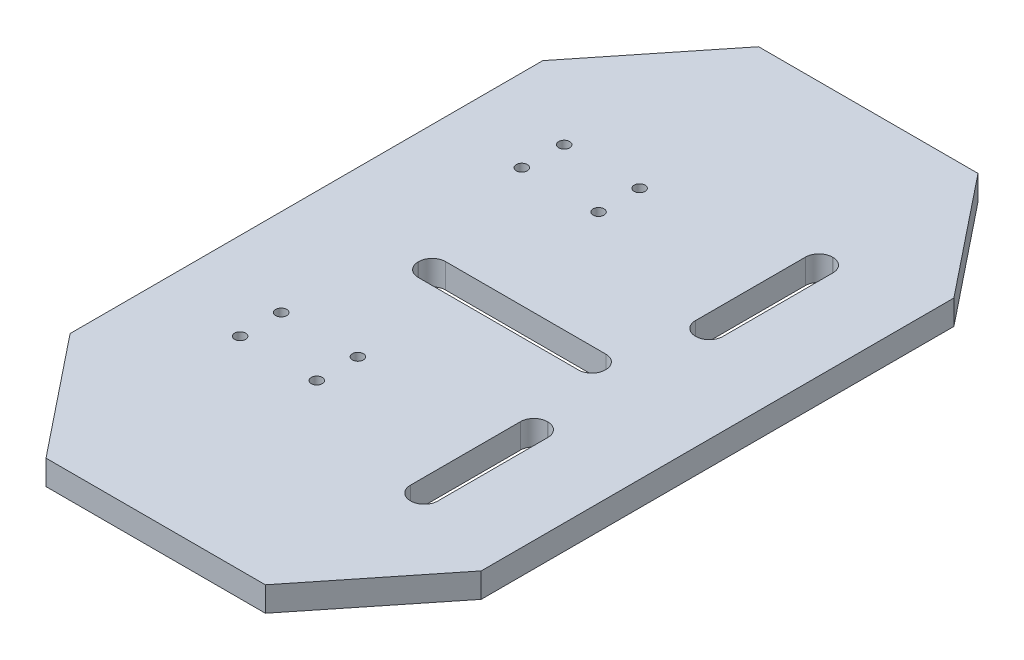
SolidWorks part; units mm, degrees
material "ABS"
ref_plane "Front Plane" through (0, 0, 0) normal (0, 0, 1) x (1, 0, 0)
ref_plane "Top Plane" through (0, 0, 0) normal (0, 1, 0) x (1, 0, 0)
ref_plane "Right Plane" through (0, 0, 0) normal (1, 0, 0) x (0, 0, -1)
other "Center of Mass"
sketch "Sketch1" plane through (0, 0, 0) normal (0, 1, 0) x (1, 0, 0)
  line L0 (-37.5, -43.1177) -> (-20.0119, -65)
  line L1 (-20.0119, -65) -> (20.0119, -65)
  line L2 (-37.5, -43.1177) -> (-37.5, 43.1177)
  line L3 (-20.0119, 65) -> (20.0119, 65)
  line L4 (37.5, -43.1177) -> (37.5, 43.1177)
  line L5 (-30.8066, -51.493) -> (30.8066, 51.493) construction
  line L6 (-32.7951, 49.0048) -> (32.7951, -49.0048) construction
  line L7 (-114.8204, 0) -> (150.9847, 0) construction
  line L8 (0, -72.5189) -> (0, 84.1411) construction
  line L9 (37.5, -43.1177) -> (20.0119, -65)
  line L10 (37.5, 43.1177) -> (20.0119, 65)
  line L11 (-37.5, 43.1177) -> (-20.0119, 65)
  point P0 (0, 0)
  dimension "D1" = 75
  dimension "D2" = 130
  dimension "D3" = 40.0238
  dimension "D4" = 86.2354
extrude "Boss-Extrude1" add sketch "Sketch1" along normal blind 4.5
sketch "Sketch5" plane through (0, 4.5, 0) normal (0, 1, 0) x (1, 0, 0)
  line L0 (-100.8141, 0) -> (111.641, 0) construction
  line L1 (20, 65) -> (20, -65) construction
  line L2 (-14.6202, -2.5) -> (14.6202, -2.5)
  line L3 (-17.0702, -0.05) -> (-17.0702, 0.05)
  line L4 (-14.6202, 2.5) -> (14.6202, 2.5)
  line L5 (17.0702, -0.05) -> (17.0702, 0.05)
  line L6 (-17.0702, -2.5) -> (17.0702, 2.5) construction
  line L7 (-17.0702, 2.5) -> (17.0702, -2.5) construction
  line L8 (20.0119, 65) -> (-20.0119, 65) construction
  line L9 (-20.0119, -65) -> (20.0119, -65) construction
  line L10 (20, 65) -> (20, 0) construction
  line L11 (20, 0) -> (20, -65) construction
  line L12 (19.95, -38.5) -> (20.05, -38.5)
  line L13 (19.95, 13.5) -> (20.05, 13.5)
  line L14 (17.5, 15.95) -> (17.5, 36.05)
  line L15 (19.95, 38.5) -> (20.05, 38.5)
  line L16 (22.5, 15.95) -> (22.5, 36.05)
  line L17 (17.5, 13.5) -> (22.5, 38.5) construction
  line L18 (17.5, 38.5) -> (22.5, 13.5) construction
  line L19 (17.5, -15.95) -> (17.5, -36.05)
  line L20 (19.95, -13.5) -> (20.05, -13.5)
  line L21 (22.5, -15.95) -> (22.5, -36.05)
  line L22 (37.5, -43.1177) -> (37.5, 43.1177) construction
  arc A0 (19.95, -38.5) -> (17.5, -36.05) centre (19.95, -36.05) cw
  arc A1 (20.05, -38.5) -> (22.5, -36.05) centre (20.05, -36.05) ccw
  arc A2 (17.5, -15.95) -> (19.95, -13.5) centre (19.95, -15.95) cw
  arc A3 (20.05, -13.5) -> (22.5, -15.95) centre (20.05, -15.95) cw
  arc A4 (-14.6202, -2.5) -> (-17.0702, -0.05) centre (-14.6202, -0.05) cw
  arc A5 (-17.0702, 0.05) -> (-14.6202, 2.5) centre (-14.6202, 0.05) cw
  arc A6 (14.6202, 2.5) -> (17.0702, 0.05) centre (14.6202, 0.05) cw
  arc A7 (14.6202, -2.5) -> (17.0702, -0.05) centre (14.6202, -0.05) ccw
  arc A8 (20.05, 13.5) -> (22.5, 15.95) centre (20.05, 15.95) ccw
  arc A9 (19.95, 13.5) -> (17.5, 15.95) centre (19.95, 15.95) cw
  arc A10 (17.5, 36.05) -> (19.95, 38.5) centre (19.95, 36.05) cw
  arc A11 (20.05, 38.5) -> (22.5, 36.05) centre (20.05, 36.05) cw
  point P3 (0, 0)
  point P14 (20, 0)
  point P15 (20, 26)
  point P17 (20, -26)
  point P18 (20, 26)
  point P31 (17.5, -38.5)
  point P34 (22.5, -38.5)
  point P37 (17.5, -13.5)
  point P40 (22.5, -13.5)
  dimension "D7" = 2.45
  dimension "D1" = 5
  dimension "D2" = 26
  dimension "D3" = 26
  dimension "D4" = 5
  dimension "D5" = 25
  dimension "D6" = 15
extrude "Cut-Extrude2" cut sketch "Sketch5" against normal blind 10
sketch "Sketch7" plane through (0, 4.5, 0) normal (0, 1, 0) x (1, 0, 0)
  line L0 (-37.5, 43.1177) -> (-37.5, -43.1177) construction
  line L1 (20.0119, 65) -> (-20.0119, 65) construction
  line L2 (-20.0119, -65) -> (20.0119, -65) construction
  line L4 (-29.5, 17.035) -> (-29.5, 35.535)
  line L5 (-1.5, 17.035) -> (-29.5, 17.035)
  line L6 (-1.5, 35.535) -> (-29.5, 35.535)
  line L7 (-1.5, 17.035) -> (-1.5, 35.535)
  line L11 (-15.5, 43.5449) -> (-15.5, 10.5144) construction
  line L12 (-22.5, 43.5449) -> (-22.5, 10.5144) construction
  line L13 (-22.2676, 32.535) -> (-22.2676, 25.035) construction
  line L14 (-23.7676, 28.785) -> (4.2324, 28.785) construction
  circle A0 centre (-22.2676, 31.79) radius 1
  circle A1 centre (-8.5, 31.79) radius 1
  circle A2 centre (-22.5, 24.29) radius 1
  circle A3 centre (-8.5, 24.29) radius 1
  circle A4 centre (-7.57, -20.54) radius 1
  circle A5 centre (-21.57, -20.54) radius 1
  circle A6 centre (-7.57, -28.04) radius 1
  circle A7 centre (-21.57, -28.04) radius 1
  circle A8 centre (-8.5, 31.79) radius 2
  circle A9 centre (-8.5, 24.29) radius 2
  circle A10 centre (-22.5, 24.29) radius 2
  circle A11 centre (-22.2676, 31.79) radius 2
  circle A12 centre (-21.57, -28.04) radius 2
  circle A13 centre (-21.57, -20.54) radius 2
  circle A14 centre (-7.57, -20.54) radius 2
  circle A15 centre (-7.57, -28.04) radius 2
  point P12 (-16.7676, 25.035)
  point P17 (-22.5, 31.79)
  dimension "D5" = 2
  dimension "D22" = 2
  dimension "D23" = 2
  dimension "D24" = 2
  dimension "D25" = 2
  dimension "D26" = 4
  dimension "D27" = 4
  dimension "D28" = 4
  dimension "D29" = 4
  dimension "D30" = 4
  dimension "D31" = 4
  dimension "D32" = 4
  dimension "D33" = 4
  dimension "D2" = 7
  dimension "D3" = 14
  dimension "D4" = 36.96
  dimension "D6" = 28
  dimension "D7" = 8
  dimension "D8" = 14
  dimension "D9" = 14
  dimension "D10" = 7.5
  dimension "D11" = 7.5
  dimension "D12" = 7
  dimension "D13" = 0.2324
  dimension "D14" = 28.785
  dimension "D15" = 28
  dimension "D16" = 33.21
  dimension "D17" = 33.21
  dimension "D18" = 33.21
  dimension "D19" = 7.5
  dimension "D20" = 36.96
  dimension "D21" = 7.5
  dimension "D34" = 15.93
  dimension "D35" = 14
extrude "Cut-Extrude3" cut sketch "Sketch7" against normal blind 5 contours A3 | A2 | A0 | A5 | A7 | A6 | A4 | A1
sketch "Sketch8" plane through (0, 4.5, 0) normal (0, 1, 0) x (1, 0, 0)
  line L0 (1.65, 0) -> (-1.65, 0) construction
  circle A4 centre (-8.5, 31.79) radius 2
  circle A5 centre (-8.5, 24.29) radius 2
  circle A6 centre (-22.5, 24.29) radius 2
  circle A7 centre (-22.2676, 31.79) radius 2
  dimension "D5" = 4
  dimension "D6" = 4
  dimension "D7" = 4
  dimension "D8" = 4
  dimension "D9" = 31.79
sketch "Sketch11" plane through (0, 0, 0) normal (0, -1, 0) x (1, 0, 0)
  circle A0 centre (-7.57, 28.04) radius 2
  circle A1 centre (-7.57, 20.54) radius 2
  circle A2 centre (-21.57, 28.04) radius 2
  circle A3 centre (-21.57, 20.54) radius 2
  circle A4 centre (-8.5, -24.29) radius 2
  circle A5 centre (-8.5, -31.79) radius 2
  circle A6 centre (-22.5, -24.29) radius 2
  circle A7 centre (-22.2676, -31.79) radius 2
  circle M2 centre (-8.5, -24.29) radius 1
  circle M36 centre (-21.57, 20.54) radius 1
  circle M39 centre (-7.57, 20.54) radius 1
  circle M40 centre (-8.5, -31.79) radius 1
  dimension "D1" = 4
  dimension "D2" = 4
  dimension "D3" = 4
  dimension "D4" = 4
  dimension "D5" = 4
  dimension "D6" = 4
  dimension "D7" = 4
  dimension "D8" = 4
extrude "Cut-Extrude4" cut sketch "Sketch11" against normal blind 1.65 contours A1 M39 | A3 M36 | A4 M2 | A5 M40 | A0 | A2 | A7 | A6
